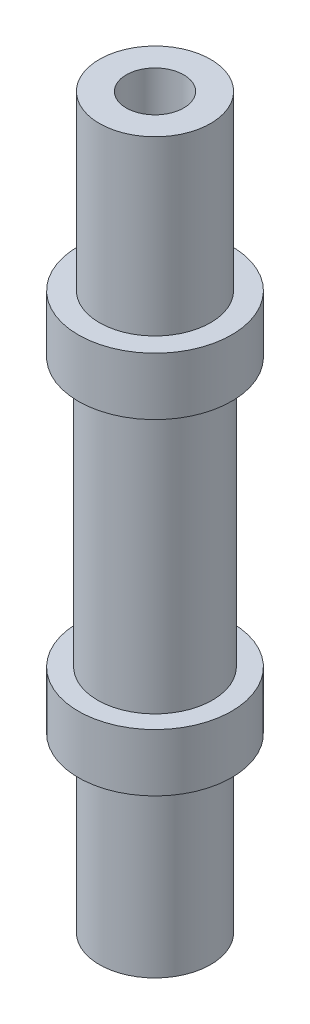
SolidWorks part; units mm, degrees
ref_plane "Front Plane" through (0, 0, 0) normal (0, 0, 1) x (1, 0, 0)
ref_plane "Top Plane" through (0, 0, 0) normal (0, 1, 0) x (1, 0, 0)
ref_plane "Right Plane" through (0, 0, 0) normal (1, 0, 0) x (0, 0, -1)
sketch "Sketch1" plane through (0, 0, 0) normal (0, 1, 0) x (1, 0, 0)
  circle A0 centre (0, 0) radius 3
  dimension "D1" = 6
extrude "Boss-Extrude1" add sketch "Sketch1" along normal mid plane 14
sketch "Sketch2" plane through (0, -7, 0) normal (0, -1, 0) x (1, 0, 0)
  circle A0 centre (0, 0) radius 4
  dimension "D1" = 8
extrude "Boss-Extrude2" add sketch "Sketch2" along normal blind 3
sketch "Sketch3" plane through (0, 7, 0) normal (0, 1, 0) x (1, 0, 0)
  circle A0 centre (0, 0) radius 4
  dimension "D1" = 8
extrude "Boss-Extrude3" add sketch "Sketch3" along normal blind 3
sketch "Sketch4" plane through (0, -10, 0) normal (0, -1, 0) x (1, 0, 0)
  circle A0 centre (0, 0) radius 2.9
  circle A1 centre (0, 0) radius 1.5
  dimension "D1" = 5.8
  dimension "D2" = 3
extrude "Boss-Extrude5" add sketch "Sketch4" along normal blind 9
sketch "Sketch5" plane through (0, 10, 0) normal (0, 1, 0) x (1, 0, 0)
  circle A0 centre (0, 0) radius 2.9
  circle A1 centre (0, 0) radius 1.5
  dimension "D1" = 5.8
  dimension "D2" = 3
extrude "Boss-Extrude6" add sketch "Sketch5" along normal blind 9
